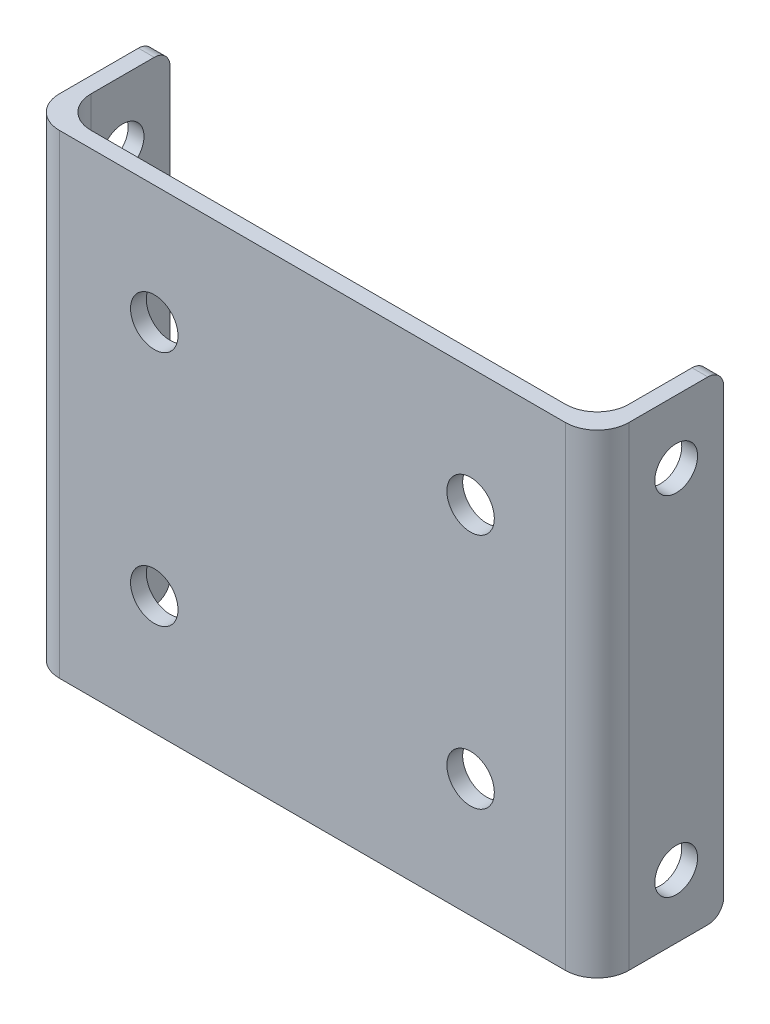
SolidWorks part; units mm, degrees
material "1060 Alloy"
ref_plane "Front Plane" through (0, 0, 0) normal (0, 0, 1) x (1, 0, 0)
ref_plane "Top Plane" through (0, 0, 0) normal (0, 1, 0) x (1, 0, 0)
ref_plane "Right Plane" through (0, 0, 0) normal (1, 0, 0) x (0, 0, -1)
sketch "Sketch1" plane through (0, 0, 0) normal (0, 1, 0) x (1, 0, 0)
  line L1 (-21.5, 0.5) -> (12.5, 0.5)
  line L2 (-22.5, 0.5) -> (-22.5, -0.5)
  line L3 (-22.5, -0.5) -> (13.5, -0.5)
  line L4 (13.5, 0.5) -> (13.5, -0.5)
  line L8 (13.5, 0.5) -> (13.5, 7.5)
  line L9 (13.5, 7.5) -> (12.5, 7.5)
  line L10 (12.5, 0.5) -> (12.5, 7.5)
  line L12 (-22.5, 0.5) -> (-22.5, 7.5)
  line L13 (-22.5, 7.5) -> (-21.5, 7.5)
  line L14 (-21.5, 0.5) -> (-21.5, 7.5)
  point P0 (0, 0)
  dimension "D1" = 36
  dimension "D2" = 1
  dimension "D3" = 1
  dimension "D4" = 1
  dimension "D5" = 7
  dimension "D6" = 7
  dimension "D7" = 1
extrude "Boss-Extrude1" add sketch "Sketch1" along normal blind 30
fillet "Fillet2" radius 2 4 edges at (-22.5, 15, 0.5) (-21.5, 15, -0.5) (13.5, 15, 0.5) (12.5, 15, -0.5)
sketch "Sketch3" plane through (0, 0, 0.5) normal (0, 0, 1) x (1, 0, 0)
  line L0 (-4.5, 22.5) -> (-14.5, 22.5)
  line L1 (-4.5, 22.5) -> (5.5, 22.5)
  line L2 (-4.5, 30) -> (-4.5, 22.5)
  line L3 (-20.5, 30) -> (11.5, 30) construction
  line L6 (-4.5, 0) -> (-4.5, 7.5)
  line L7 (-20.5, 0) -> (11.5, 0) construction
  line L8 (-4.5, 7.5) -> (-14.5, 7.5)
  line L9 (-4.5, 7.5) -> (5.5, 7.5)
  circle A0 centre (-14.5, 22.5) radius 1.5
  circle A1 centre (5.5, 22.5) radius 1.5
  circle A2 centre (-14.5, 7.5) radius 1.5
  circle A3 centre (5.5, 7.5) radius 1.5
  dimension "D3" = 10
  dimension "D4" = 3
  dimension "D9" = 3
  dimension "D10" = 3
  dimension "D5" = 3
  dimension "D2" = 10
  dimension "D6" = 7.5
  dimension "D7" = 10
  dimension "D8" = 10
  dimension "D11" = 7.5
extrude "Cut-Extrude4" cut sketch "Sketch3" against normal through all
sketch "Sketch4" plane through (13.5, 0, 0) normal (1, 0, 0) x (0, 0, -1)
  line L0 (4.5, 30) -> (4.5, 26)
  line L2 (1.5, 30) -> (7.5, 30) construction
  line L6 (4.5, 0) -> (4.5, 4)
  line L10 (1.5, 0) -> (7.5, 0) construction
  circle A0 centre (4.5, 26) radius 1.35
  circle A1 centre (4.5, 4) radius 1.35
  dimension "D3" = 2.7
  dimension "D4" = 2.7
  dimension "D1" = 4
  dimension "D2" = 4
extrude "Cut-Extrude3" cut sketch "Sketch4" against normal through all
fillet "Fillet3" radius 1 4 edges at (-22, 30, -7.5) (-22, 0, -7.5) (13, 0, -7.5) (13, 30, -7.5)
